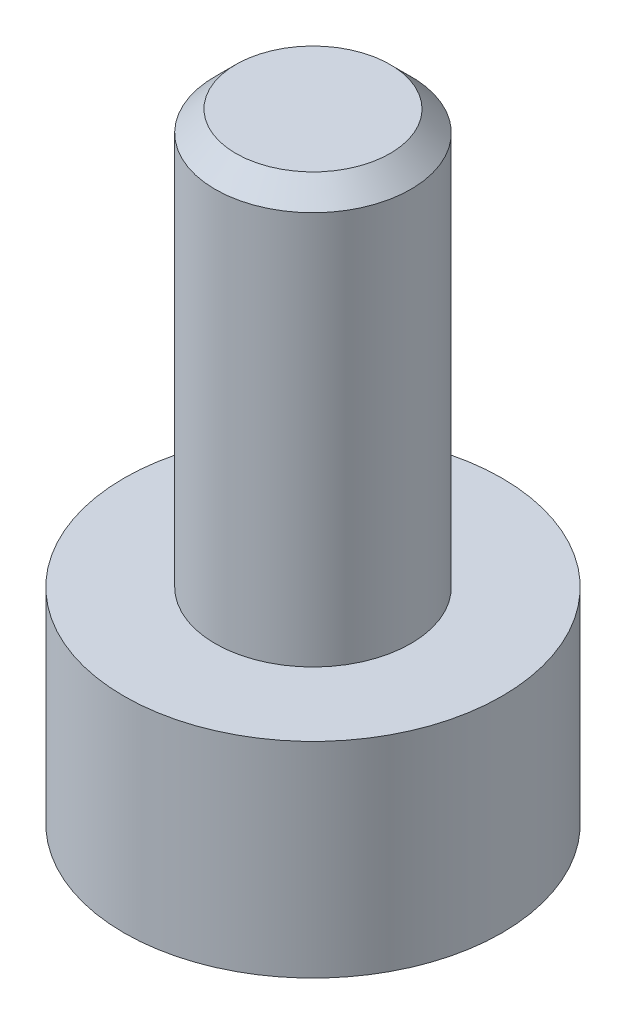
SolidWorks part; units mm, degrees
ref_plane "Front Plane" through (0, 0, 0) normal (0, 0, 1) x (1, 0, 0)
ref_plane "Top Plane" through (0, 0, 0) normal (0, 1, 0) x (1, 0, 0)
ref_plane "Right Plane" through (0, 0, 0) normal (1, 0, 0) x (0, 0, -1)
sketch "Sketch1" plane through (0, 0, 0) normal (0, 1, 0) x (1, 0, 0)
  circle A0 centre (0, 0) radius 1.825
  dimension "D1" = 3.65
extrude "Boss-Extrude1" add sketch "Sketch1" along normal blind 1.98
sketch "Sketch2" plane through (0, 1.98, 0) normal (0, 1, 0) x (1, 0, 0)
  circle A0 centre (0, 0) radius 0.945
  dimension "D1" = 1.89
extrude "Boss-Extrude2" add sketch "Sketch2" along normal blind 4
sketch "Sketch3" plane through (0, 0, 0) normal (0, -1, 0) x (1, 0, 0)
  line L1 (0.459, -0.795) -> (0.918, 0)
  line L2 (0.918, 0) -> (0.459, 0.795)
  line L3 (0.459, 0.795) -> (-0.459, 0.795)
  line L4 (-0.459, 0.795) -> (-0.918, 0)
  line L5 (-0.918, 0) -> (-0.459, -0.795)
  line L6 (-0.459, -0.795) -> (0.459, -0.795)
  circle A0 centre (0, 0) radius 0.795 construction
  dimension "D1" = 1.59
extrude "Cut-Extrude1" cut sketch "Sketch3" against normal blind 1
chamfer "Chamfer1" distance 0.2 angle 45 1 edges at (0, 5.98, 0.945)
